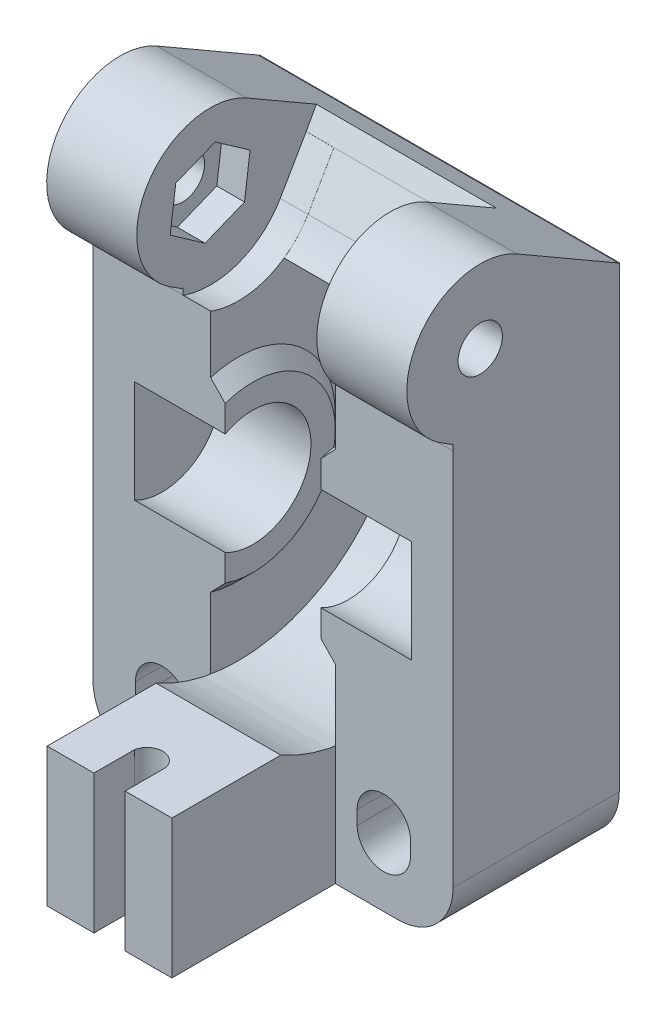
SolidWorks part; units mm, degrees
ref_plane "Front" through (0, 0, 0) normal (0, 0, 1) x (1, 0, 0)
ref_plane "Top" through (0, 0, 0) normal (0, 1, 0) x (1, 0, 0)
ref_plane "Right" through (0, 0, 0) normal (1, 0, 0) x (0, 0, -1)
ref_plane "Plane1" through (-2, 0, 0) normal (1, 0, 0) x (0, 0, -1)
sketch "Sketch1" plane through (-2, 0, 0) normal (1, 0, 0) x (0, 0, -1)
  line L7 (-20.9502, 5.0077) -> (-22.8246, 1.7613)
  line L8 (-17.8475, 5.0077) -> (-20.9502, 5.0077)
  line L9 (-17.8475, -5.0346) -> (-17.8475, 5.0077)
  spline S2 degree 3 poles (-22.8246, 1.7613) (-22.9072, 1.634) (-22.9899, 1.5067) (-23.0726, 1.3794) (-23.0909, 1.3512) (-23.1276, 1.2947) (-23.1871, 1.2127) (-23.2295, 1.1604) (-23.2507, 1.1342) (-23.3144, 1.0556) (-23.3781, 0.9769) (-23.4418, 0.8983) (-23.463, 0.8721) (-23.5054, 0.8198) (-23.5732, 0.7445) (-23.6208, 0.6969) (-23.6446, 0.673) (-23.7161, 0.6015) (-23.7877, 0.53) (-23.8592, 0.4584) (-23.8831, 0.4346) (-23.9307, 0.387) (-24.006, 0.3192) (-24.0583, 0.2768) (-24.0845, 0.2556) (-24.1928, 0.1679) (-24.3011, 0.0802) (-24.4094, -0.0075) (-24.4158, -0.0127) (-24.4287, -0.0231) (-24.4488, -0.0377) (-24.4627, -0.0468) (-24.4697, -0.0513) (-24.4906, -0.0648) (-24.5114, -0.0784) (-24.5323, -0.0919) (-24.5351, -0.0938) (-24.5408, -0.0974) (-24.5373, -0.1193) (-24.5308, -0.121) (-24.5276, -0.1219) (-24.4335, -0.1471) (-24.3394, -0.1723) (-24.2454, -0.1975) (-24.2219, -0.2038) (-24.1748, -0.2165) (-24.1051, -0.2391) (-24.0596, -0.2566) (-24.0368, -0.2653) (-23.7778, -0.3647) (-23.5188, -0.4642) (-23.2598, -0.5636) (-23.1948, -0.5886) (-23.0647, -0.6385) (-22.8732, -0.7238) (-22.749, -0.7871) (-22.6869, -0.8187) (-22.5004, -0.9137) (-22.3138, -1.0088) (-22.1273, -1.1038) (-22.0652, -1.1354) (-21.941, -1.1987) (-21.7595, -1.3035) (-21.6426, -1.3794) (-21.5842, -1.4174) (-21.4086, -1.5314) (-21.233, -1.6454) (-21.0575, -1.7594) (-20.999, -1.7974) (-20.8821, -1.8733) (-20.7125, -1.9965) (-20.6042, -2.0842) (-20.5501, -2.1281) (-20.3874, -2.2598) (-20.2247, -2.3916) (-20.062, -2.5233) (-20.0078, -2.5672) (-19.8995, -2.6549) (-19.7437, -2.7952) (-19.6452, -2.8937) (-19.5959, -2.943) (-19.4479, -3.091) (-19.2999, -3.239) (-19.1518, -3.387) (-19.1025, -3.4363) (-19.004, -3.5348) (-18.8637, -3.6906) (-18.776, -3.7989) (-18.7322, -3.8531) (-18.5626, -4.0625) (-18.3931, -4.2718) (-18.2236, -4.4812) (-18.2049, -4.5043) (-18.1675, -4.5505) (-18.1149, -4.6228) (-18.0826, -4.6727) (-18.0664, -4.6976) (-17.9934, -4.8099) (-17.9205, -4.9222) (-17.8475, -5.0346) knots 0 0 0 0 0.041251 0.041251 0.041251 0.050405 0.059559 0.068713 0.068713 0.068713 0.096213 0.096213 0.096213 0.105366 0.114519 0.123672 0.123672 0.123672 0.151169 0.151169 0.151169 0.160322 0.169476 0.17863 0.17863 0.17863 0.216499 0.216499 0.216499 0.21875 0.221001 0.223253 0.223253 0.223253 0.230016 0.230016 0.230016 0.230933 0.23185 0.232767 0.232767 0.232767 0.25923 0.25923 0.25923 0.265853 0.272476 0.2791 0.2791 0.2791 0.354495 0.354495 0.354495 0.373434 0.392373 0.411312 0.411312 0.411312 0.468206 0.468206 0.468206 0.487145 0.506083 0.525022 0.525022 0.525022 0.581917 0.581917 0.581917 0.600856 0.619795 0.638734 0.638734 0.638734 0.69563 0.69563 0.69563 0.714568 0.733507 0.752446 0.752446 0.752446 0.809338 0.809338 0.809338 0.828277 0.847216 0.866155 0.866155 0.866155 0.939366 0.939366 0.939366 0.947444 0.955522 0.9636 0.9636 0.9636 1 1 1 1
  dimension "D7" = 10.0423
  dimension "D8" = 3.1027
extrude "Boss-Extrude1" add sketch "Sketch1" against normal blind 4.5
sketch "Sketch2" plane through (-2, 0, 0) normal (1, 0, 0) x (0, 0, -1)
  line L0 (-22.8291, 1.7616) -> (-20.9549, 5.0077)
  line L1 (-20.9549, 5.0077) -> (-17.852, 5.0077)
  line L2 (-17.852, 5.0077) -> (-17.852, -0.1112)
  line L3 (-17.852, -0.1112) -> (-17.852, -4.9235)
  line L4 (-17.852, -4.9235) -> (-17.852, -32.0637)
  line L5 (-17.852, -32.0637) -> (-29.852, -32.0637)
  line L6 (-29.852, -32.0637) -> (-29.852, -0.7747)
  line L7 (-17.8475, -5.0346) -> (-17.8475, 5.0077) construction
  line L8 (-17.8475, 5.0077) -> (-20.9502, 5.0077) construction
  spline S0 degree 2 poles (-22.8291, 1.7616) (-23.096, 1.3506) (-23.1053, 1.3366) (-23.1431, 1.2791) (-23.1779, 1.2326) (-23.2039, 1.1979) (-23.2564, 1.1331) (-23.3362, 1.0346) (-23.4159, 0.9361) (-23.4794, 0.8577) (-23.496, 0.8379) (-23.5377, 0.788) (-23.5804, 0.7432) (-23.6014, 0.7211) (-23.6336, 0.6889) (-23.6391, 0.6834) (-23.6874, 0.6351) (-23.7232, 0.5993) (-23.7591, 0.5634) (-23.7996, 0.5229) (-23.8487, 0.4738) (-23.9137, 0.4089) (-23.939, 0.3849) (-23.9841, 0.3423) (-24.034, 0.3009) (-24.0525, 0.2855) (-24.1323, 0.2209) (-24.2308, 0.1411) (-24.3293, 0.0614) (-24.4234, -0.0149) (-24.4278, -0.0183) (-24.441, -0.0287) (-24.4533, -0.0371) (-24.4605, -0.0421) (-24.4798, -0.0546) (-24.514, -0.0768) (-24.5329, -0.0891) (-24.5682, -0.112) (-24.7455, -0.2271) (-24.8123, -0.2705) (-24.8518, -0.2961) (-24.8889, -0.3203) (-24.9051, -0.3304) (-24.9329, -0.3478) (-24.9595, -0.3628) (-24.9993, -0.3852) (-25.0716, -0.4222) (-25.0772, -0.425) (-25.1845, -0.4797) (-25.3931, -0.586) (-25.4104, -0.5947) (-25.4709, -0.6248) (-25.5255, -0.6479) (-25.5445, -0.656) (-25.5646, -0.664) (-25.5882, -0.6735) (-25.6434, -0.6946) (-25.7617, -0.74) (-25.88, -0.7854) (-25.9719, -0.8207) (-25.9985, -0.8303) (-26.0589, -0.8522) (-26.1191, -0.8697) (-26.1485, -0.8782) (-26.2071, -0.8939) (-26.2345, -0.9013) (-26.2658, -0.9097) (-26.2941, -0.9173) (-26.3637, -0.9359) (-26.4427, -0.9571) (-26.4861, -0.9687) (-26.5454, -0.9846) (-26.5678, -0.9903) (-26.5901, -0.996) (-26.6089, -1.0004) (-26.6683, -1.0142) (-26.7333, -1.0252) (-26.7546, -1.0288) (-26.8584, -1.0452) (-27.1048, -1.0842) (-27.1087, -1.0848) (-27.1863, -1.0971) (-27.2343, -1.1024) (-27.2898, -1.1086) (-27.3607, -1.1125) (-27.3733, -1.1132) (-27.6138, -1.1258) (-27.7274, -1.1318) (-27.7404, -1.1324) (-27.8114, -1.1358) (-27.8672, -1.1354) (-27.9151, -1.135) (-27.9939, -1.1309) (-27.9975, -1.1307) (-28.1204, -1.1243) (-28.3516, -1.1121) (-28.3735, -1.1107) (-28.4397, -1.1065) (-28.4998, -1.0988) (-28.5198, -1.0963) (-28.5417, -1.0931) (-28.5643, -1.0898) (-28.6251, -1.0801) (-28.7503, -1.0603) (-28.8755, -1.0405) (-28.9701, -1.0255) (-29.0005, -1.02) (-29.0628, -1.0087) (-29.1246, -0.9933) (-29.1517, -0.9865) (-29.2716, -0.9544) (-29.3181, -0.9419) (-29.3695, -0.9281) (-29.6067, -0.8645) (-29.6142, -0.8624) (-29.645, -0.8538) (-29.6745, -0.8428) (-29.6822, -0.8399) (-29.7337, -0.8201) (-29.8051, -0.7928) (-29.852, -0.7747) knots 0 0 0 0.0625 0.0625 0.078125 0.078125 0.09375 0.09375 0.125 0.125 0.140625 0.140625 0.15625 0.15625 0.165625 0.165625 0.175 0.175 0.1875 0.1875 0.203125 0.203125 0.21875 0.21875 0.234375 0.234375 0.25 0.25 0.28125 0.28125 0.296875 0.296875 0.300781 0.300781 0.304688 0.304688 0.3125 0.3125 0.34375 0.34375 0.359375 0.359375 0.367188 0.367188 0.375 0.375 0.390625 0.390625 0.40625 0.40625 0.4375 0.4375 0.453125 0.453125 0.458333 0.458333 0.46875 0.46875 0.5 0.5 0.515625 0.515625 0.53125 0.53125 0.5425 0.5425 0.55 0.55 0.5625 0.5625 0.578125 0.578125 0.588542 0.588542 0.59375 0.59375 0.609375 0.609375 0.625 0.625 0.65625 0.65625 0.671875 0.671875 0.6875 0.6875 0.71875 0.71875 0.734375 0.734375 0.75 0.75 0.765625 0.765625 0.78125 0.78125 0.8125 0.8125 0.828125 0.828125 0.833333 0.833333 0.84375 0.84375 0.875 0.875 0.890625 0.890625 0.90625 0.90625 0.925 0.925 0.9375 0.9375 0.96875 0.96875 0.976562 0.976562 0.984375 0.984375 1 1 1
  dimension "D1" = 0.0045
  dimension "D2" = 3.1074
  dimension "D3" = 4.9816
  dimension "D4" = 12.0045
  dimension "D5" = 3.2461
  dimension "D6" = 5.119
  dimension "D7" = 5.7825
  dimension "D8" = 9.9312
  dimension "D9" = 37.0714
extrude "Boss-Extrude2" add sketch "Sketch2" along normal blind 8.5
sketch "Sketch3" plane through (6.5, 0, 0) normal (1, 0, 0) x (0, 0, -1)
  line L0 (-25.2398, 9.2472) -> (-17.8969, 5.0077)
  line L1 (-17.8969, 5.0077) -> (-17.852, 5.0077)
  line L2 (-17.852, 5.0077) -> (-17.852, -1.3448)
  line L4 (-29.852, -1.3448) -> (-29.852, -0.3041)
  line L5 (-29.852, -0.3041) -> (-29.9685, -0.3041)
  line L6 (-29.9685, -0.3041) -> (-31.0118, 0.3733)
  line L7 (-29.852, -0.7747) -> (-29.852, -32.0637) construction
  line L8 (-29.852, -32.0637) -> (-17.852, -32.0637) construction
  line L9 (-29.852, -1.3448) -> (-17.852, -1.3448)
  arc A0 (-31.0118, 0.3733) -> (-25.2398, 9.2472) centre (-27.89, 4.6569) cw
  dimension "D1" = 5.3004
  dimension "D2" = 1.962
  dimension "D3" = 4.6122
  dimension "D4" = 11.9551
  dimension "D6" = 0.1164
  dimension "D7" = 1.1598
  dimension "D8" = 31.7596
  dimension "D9" = 32.437
extrude "Boss-Extrude6" add sketch "Sketch3" against normal blind 6.5
sketch "Sketch4" plane through (-2, 0, 0) normal (-1, 0, 0) x (0, 0, 1)
  line L0 (29.852, -4.9251) -> (29.852, -18.3444)
  line L1 (29.852, -0.7747) -> (29.852, -32.0637) construction
  line L2 (29.852, -32.0637) -> (17.852, -32.0637) construction
  arc A0 (29.852, -18.3444) -> (29.852, -4.9251) centre (27.8621, -11.6347) cw
  dimension "D1" = 6.9985
  dimension "D2" = 1.9899
  dimension "D3" = 13.7193
  dimension "D4" = 20.4289
extrude "Boss-Extrude4" add sketch "Sketch4" along normal blind 1.05
sketch "Sketch19" plane through (-6.5, 0, 0) normal (-1, 0, 0) x (0, 0, 1)
  line L0 (20.9502, 5.0077) -> (20.223, 6.3507)
  line L1 (20.223, 6.3507) -> (17.8969, 5.0077)
  line L2 (17.8475, 5.0077) -> (20.9502, 5.0077) construction
  line L3 (17.8969, 5.0077) -> (20.9502, 5.0077)
  line L4 (17.8969, 5.0077) -> (25.2398, 9.2472) construction
  dimension "D1" = 2.686
extrude "Boss-Extrude8" add sketch "Sketch19" against normal up to surface (6.5 mm away) up to face at (0, 2.7148, 26.9155)
sketch "Sketch5" plane through (0, 0, 0) normal (-1, 0, 0) x (0, 0, 1)
  line L0 (28.2571, 1.6744) -> (30.7737, 3.4392)
  line L1 (30.7737, 3.4392) -> (30.3724, 6.4867)
  line L2 (30.3724, 6.4867) -> (27.523, 7.6394)
  line L3 (27.523, 7.6394) -> (25.0064, 5.8746)
  line L4 (25.0064, 5.8746) -> (25.4077, 2.8272)
  line L5 (25.4077, 2.8272) -> (28.2571, 1.6744)
  line L8 (27.523, 7.6394) -> (28.2571, 1.6744) construction
  line L9 (30.5731, 4.9629) -> (25.207, 4.3509) construction
  dimension "D1" = 6.01
  dimension "D2" = 5.4
extrude "Cut-Extrude1" cut sketch "Sketch5" against normal blind 2
draft "Draft1" type of draft neutral plane draft angle 44.789 faces to draft 1 face at (-2.525, -11.6347, 25.3578) neutral plane through (-2, -0.7854, 25.88) neutral plane normal (-1, 0, 0) parameters "D1"=44.789
hole_wizard "M3 Clearance Hole2" positions "Sketch17" profile "Sketch16" hole size "M3" standard "ANSI Metric" end condition through all
sketch "Sketch17" plane through (2, 0, 0) normal (-1, 0, 0) x (0, 0, 1)
  point P0 (27.89, 4.6569)
sketch "Sketch16" plane through (2, 4.6569, 27.89) normal (0, 1, 0) x (0, 0, 1)
  line L0 (0, 0) -> (0, 4.5)
  line L1 (0, 4.5) -> (1.6, 4.5)
  line L2 (1.6, 4.5) -> (1.6, 0)
  line L5 (1.6, 0) -> (0, 0)
  line L11 (0, -6.35) -> (0, 107.95) construction
  dimension "Thru Hole Dia." = 3.2
  dimension "Thru Hole Depth" = 4.5
hole_wizard "M8 Clearance Hole1" positions "Sketch9" profile "Sketch8" hole size "M8" standard "ANSI Metric"
sketch "Sketch9" plane through (-3.05, 0, 0) normal (-1, 0, 0) x (0, 0, 1)
  point P0 (27.8621, -11.6347)
sketch "Sketch8" plane through (-3.05, -11.6347, 27.8621) normal (0, 1, 0) x (0, 0, 1)
  line L0 (0, 0) -> (0, 6.55)
  line L1 (0, 6.55) -> (4.204, 6.55)
  line L2 (4.204, 6.55) -> (4.204, 0)
  line L5 (4.204, 0) -> (0, 0)
  line L10 (0, 6.55) -> (-4.204, 6.55) construction
  line L11 (0, -6.35) -> (0, 107.95) construction
  dimension "Hole Dia." = 8.408
  dimension "Hole Depth" = 6.55
  dimension "Drill Angle" = 180
sketch "Sketch10" plane through (-2, 0, 0) normal (-1, 0, 0) x (0, 0, 1)
  line L0 (33.7878, -22.0637) -> (41.652, -22.0637)
  line L1 (41.652, -22.0637) -> (41.652, -32.0637)
  line L2 (41.652, -32.0637) -> (17.852, -32.0637)
  line L3 (17.852, -32.0637) -> (17.852, -18.2428)
  line L6 (17.852, -32.0637) -> (17.852, -5.0276) construction
  line L7 (29.852, -32.0637) -> (17.852, -32.0637) construction
  spline S0 degree 3 poles (33.7878, -22.0637) (33.5241, -22.198) (33.2603, -22.3324) (32.9966, -22.4668) (32.9363, -22.4975) (32.8156, -22.559) (32.6293, -22.6409) (32.5029, -22.6894) (32.4397, -22.7137) (32.2442, -22.7887) (32.0488, -22.8638) (31.8534, -22.9388) (31.7883, -22.9638) (31.6582, -23.0137) (31.4588, -23.0785) (31.3242, -23.1146) (31.2569, -23.1326) (30.9939, -23.2031) (30.7309, -23.2736) (30.4679, -23.344) (30.4411, -23.3512) (30.3874, -23.3656) (30.3056, -23.383) (30.2507, -23.3917) (30.2232, -23.3961) (30.1407, -23.4091) (30.0582, -23.4222) (29.9758, -23.4353) (29.9413, -23.4407) (29.8724, -23.4516) (29.769, -23.468) (29.7001, -23.4789) (29.6656, -23.4844) (29.5413, -23.5041) (29.417, -23.5237) (29.2928, -23.5434) (29.2377, -23.5522) (29.1274, -23.5696) (28.9599, -23.5806) (28.8485, -23.5865) (28.7928, -23.5894) (28.5837, -23.6003) (28.3747, -23.6113) (28.1656, -23.6222) (28.096, -23.6259) (27.9568, -23.6332) (27.7472, -23.6332) (27.608, -23.6259) (27.5384, -23.6222) (27.3294, -23.6113) (27.1203, -23.6003) (26.9113, -23.5894) (26.8417, -23.5857) (26.7025, -23.5784) (26.494, -23.5565) (26.3564, -23.5347) (26.2875, -23.5238) (26.0808, -23.4911) (25.874, -23.4583) (25.6672, -23.4256) (25.5984, -23.4147) (25.4608, -23.3929) (25.2557, -23.3493) (25.1211, -23.3132) (25.0538, -23.2952) (24.8516, -23.241) (24.6494, -23.1868) (24.4471, -23.1326) (24.3798, -23.1146) (24.2452, -23.0785) (24.0458, -23.0137) (23.9157, -22.9638) (23.8507, -22.9388) (23.6552, -22.8638) (23.4598, -22.7887) (23.2644, -22.7137) (23.1993, -22.6887) (23.0692, -22.6388) (22.8777, -22.5535) (22.7535, -22.4902) (22.6914, -22.4586) (22.5049, -22.3636) (22.3183, -22.2685) (22.1318, -22.1735) (22.0697, -22.1419) (21.9455, -22.0786) (21.764, -21.9738) (21.6471, -21.8979) (21.5887, -21.8599) (21.4131, -21.7459) (21.2375, -21.6319) (21.062, -21.5179) (21.0035, -21.4799) (20.8866, -21.404) (20.717, -21.2808) (20.6087, -21.1931) (20.5546, -21.1492) (20.3919, -21.0175) (20.2292, -20.8857) (20.0665, -20.754) (20.0123, -20.7101) (19.904, -20.6224) (19.7482, -20.4821) (19.6497, -20.3836) (19.6004, -20.3343) (19.4524, -20.1863) (19.3044, -20.0383) (19.1563, -19.8903) (19.1071, -19.841) (19.0085, -19.7425) (18.8682, -19.5867) (18.7805, -19.4784) (18.7367, -19.4242) (18.5672, -19.2149) (18.3976, -19.0055) (18.2281, -18.7961) (18.2094, -18.773) (18.172, -18.7268) (18.1194, -18.6545) (18.0871, -18.6047) (18.0709, -18.5797) (17.9979, -18.4674) (17.925, -18.3551) (17.852, -18.2428) knots 0 0 0 0 0.049231 0.049231 0.049231 0.060489 0.071747 0.083004 0.083004 0.083004 0.117821 0.117821 0.117821 0.129411 0.141001 0.152592 0.152592 0.152592 0.197875 0.197875 0.197875 0.202498 0.207122 0.211745 0.211745 0.211745 0.225635 0.225635 0.225635 0.231437 0.23724 0.243043 0.243043 0.243043 0.263971 0.263971 0.263971 0.27325 0.282529 0.291808 0.291808 0.291808 0.326624 0.326624 0.326624 0.338214 0.349804 0.361393 0.361393 0.361393 0.396211 0.396211 0.396211 0.407801 0.419391 0.430981 0.430981 0.430981 0.465798 0.465798 0.465798 0.477388 0.488978 0.500568 0.500568 0.500568 0.535385 0.535385 0.535385 0.546975 0.558566 0.570156 0.570156 0.570156 0.604974 0.604974 0.604974 0.616564 0.628154 0.639744 0.639744 0.639744 0.674561 0.674561 0.674561 0.686151 0.697741 0.70933 0.70933 0.70933 0.744148 0.744148 0.744148 0.755738 0.767328 0.778918 0.778918 0.778918 0.813736 0.813736 0.813736 0.825326 0.836916 0.848506 0.848506 0.848506 0.883322 0.883322 0.883322 0.894912 0.906502 0.918091 0.918091 0.918091 0.962894 0.962894 0.962894 0.967838 0.972781 0.977724 0.977724 0.977724 1 1 1 1
  dimension "D1" = 13.8209
  dimension "D2" = 23.8
  dimension "D3" = 7.8642
extrude "Boss-Extrude5" add sketch "Sketch10" along normal blind 4.5
sketch "Sketch11" plane through (0, -22.0637, 0) normal (0, 1, 0) x (1, 0, 0)
  line L0 (-6.5, -41.652) -> (-6.5, -33.7878) construction
  line L3 (-6.5, -41.652) -> (-2, -41.652) construction
  line L4 (-5.375, -41.652) -> (-6.5, -41.652)
  line L5 (-5.375, -38.7149) -> (-5.375, -41.652)
  line L6 (-6.5, -41.652) -> (-6.5, -37.8013)
  arc A1 (-6.5, -37.8013) -> (-5.375, -38.7149) centre (-6.5, -38.9508) cw
  dimension "D1" = 3.8507
  dimension "D2" = 1.125
  dimension "D3" = 2.9371
extrude "Cut-Extrude2" cut sketch "Sketch11" against normal through all
sketch "Sketch12" plane through (0, 0, 29.852) normal (0, 0, 1) x (1, 0, 0)
  line L0 (-0.425, -26.6387) -> (-0.425, -27.6387)
  line L1 (3.425, -27.6387) -> (3.425, -26.6387)
  arc A0 (-0.425, -27.6387) -> (3.425, -27.6387) centre (1.5, -27.6387) ccw
  arc A1 (3.425, -26.6387) -> (-0.425, -26.6387) centre (1.5, -26.6387) ccw
  dimension "D1" = 1.925
  dimension "D2" = 1
extrude "Cut-Extrude3" cut sketch "Sketch12" against normal through all
fillet "Fillet1" radius 4 1 edges at (6.5, -32.0637, 23.852)
mirror "Mirror2" about plane through (-6.5, -23.2978, 25.0637) normal (-1, 0, 0) of bodies 112
